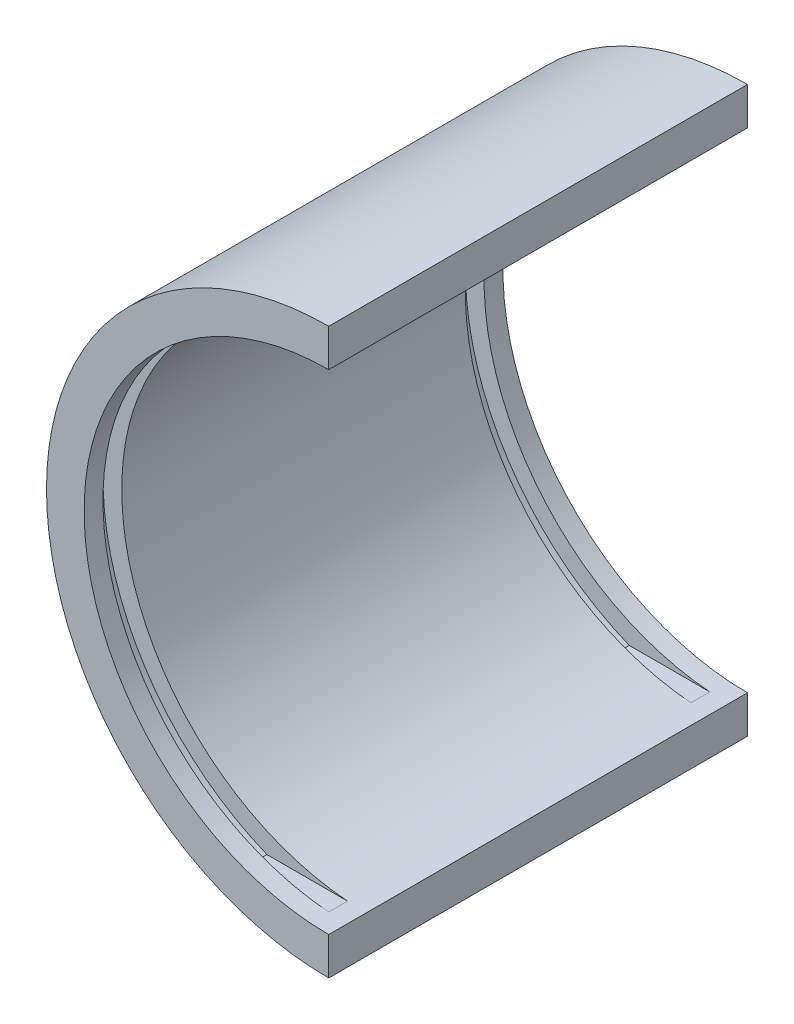
SolidWorks part; units mm, degrees
ref_plane "Front Plane" through (0, 0, 0) normal (0, 0, 1) x (1, 0, 0)
ref_plane "Top Plane" through (0, 0, 0) normal (0, 1, 0) x (1, 0, 0)
ref_plane "Right Plane" through (0, 0, 0) normal (1, 0, 0) x (0, 0, -1)
sketch "Sketch1" plane through (0, 0, 0) normal (0, 0, 1) x (1, 0, 0)
  line L0 (0, 150) -> (0, 130)
  line L1 (0, -130) -> (0, -150)
  arc A0 (0, 150) -> (0, -150) centre (0, 0) ccw
  arc A1 (0, 130) -> (0, -130) centre (0, 0) ccw
  dimension "D2" = 150
  dimension "D3" = 130
  dimension "D1" = 20
  dimension "D4" = 20
extrude "Boss-Extrude1" add sketch "Sketch1" along normal blind 222.57
sketch "Sketch2" plane through (0, 0, 222.57) normal (0, 0, 1) x (1, 0, 0)
  line L0 (-10, 139.6148) -> (-10, 129.6148) construction
  line L1 (-10, -139.6148) -> (-10, -129.6148) construction
  line L2 (0, 130) -> (0, 150) construction
  line L3 (0, -150) -> (0, -130) construction
  line L4 (-10, 129.6148) -> (-52.8422, 129.6148)
  line L5 (-10, -129.6148) -> (-52.8422, -129.6148)
  arc A0 (-52.8422, 129.6148) -> (-52.8422, -129.6148) centre (0, 0) ccw
  arc A1 (0, 130) -> (0, -130) centre (0, 0) ccw construction
  arc A2 (-10, 129.6148) -> (-10, -129.6148) centre (0, 0) ccw
  arc A3 (-10, 139.6148) -> (-52.8422, 129.6148) centre (0, 0) ccw construction
  arc A4 (-52.8422, -129.6148) -> (-10, -139.6148) centre (0, 0) ccw construction
  dimension "D3" = 10
  dimension "D1" = 10
  dimension "D2" = 10
extrude "Cut-Extrude2" cut sketch "Sketch2" against normal blind 10 from offset 10 offset against normal yes
sketch "Sketch3" plane through (0, 0, 0) normal (0, 0, -1) x (-1, 0, 0)
  line L0 (10, 139.6148) -> (10, 129.6148) construction
  line L1 (10, -139.6148) -> (10, -129.6148) construction
  line L2 (0, 130) -> (0, 150) construction
  line L3 (0, -150) -> (0, -130) construction
  line L4 (10, 129.6148) -> (52.8422, 129.6148)
  line L5 (10, -129.6148) -> (52.8422, -129.6148)
  arc A0 (52.8422, 129.6148) -> (52.8422, -129.6148) centre (0, 0) cw
  arc A1 (0, -130) -> (0, 130) centre (0, 0) ccw construction
  arc A2 (10, 129.6148) -> (10, -129.6148) centre (0, 0) cw
  arc A3 (10, 139.6148) -> (52.8422, 129.6148) centre (0, 0) cw construction
  arc A4 (52.8422, -129.6148) -> (10, -139.6148) centre (0, 0) cw construction
  point P15 (10, -134.6148)
  arc M3 (0, 130) -> (0, -130) centre (0, 0) cw
  dimension "D1" = 10
  dimension "D2" = 10
  dimension "D3" = 10
extrude "Cut-Extrude3" cut sketch "Sketch3" against normal blind 10 from offset 10 contours A0 L0 L1 M3
